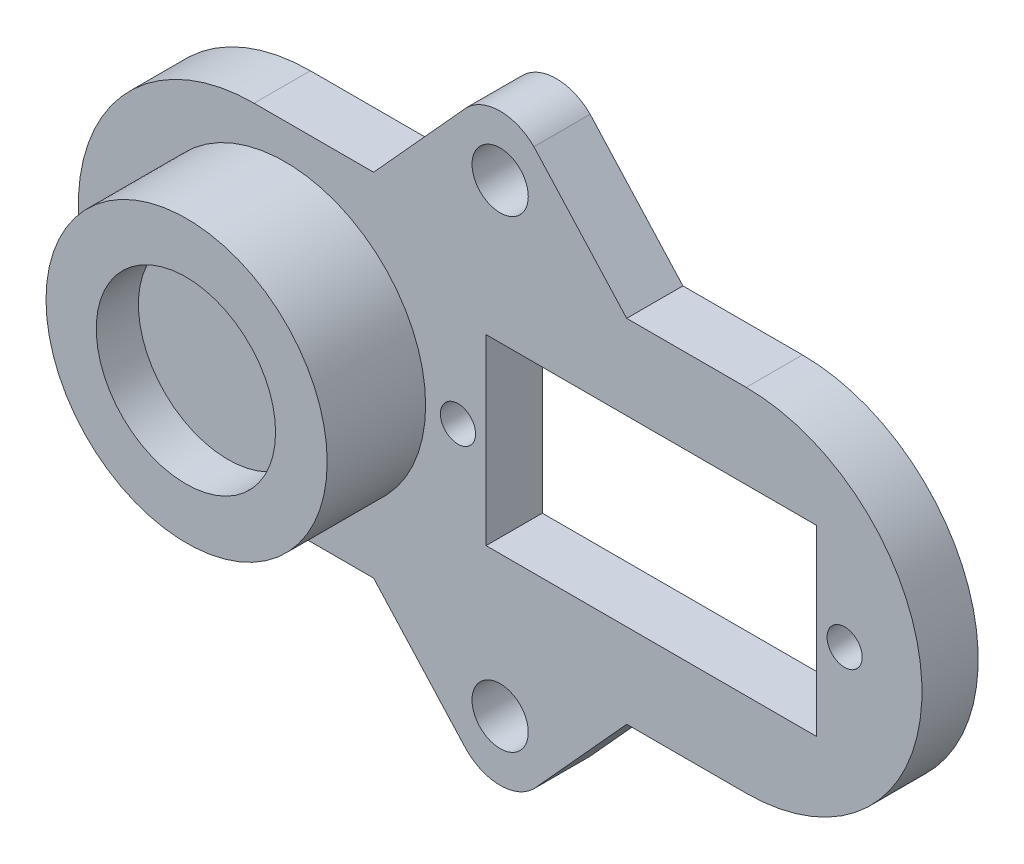
SolidWorks part; units mm, degrees
ref_plane "Front" through (0, 0, 0) normal (0, 0, 1) x (1, 0, 0)
ref_plane "Top" through (0, 0, 0) normal (0, 1, 0) x (1, 0, 0)
ref_plane "Right" through (0, 0, 0) normal (1, 0, 0) x (0, 0, -1)
sketch "Sketch1" plane through (0, 0, 0) normal (0, 0, 1) x (1, 0, 0)
  line L0 (-9, 12.5) -> (-2.401, 19.7724)
  line L1 (-17.5, 12.5) -> (-9, 12.5)
  line L5 (2.401, 19.7724) -> (9, 12.5)
  line L6 (9, 12.5) -> (17.5, 12.5)
  line L7 (-52.4135, 0) -> (76.2531, 0) construction
  line L12 (9, -12.5) -> (17.5, -12.5)
  line L13 (2.401, -19.7724) -> (9, -12.5)
  line L14 (-17.5, -12.5) -> (-9, -12.5)
  line L15 (-9, -12.5) -> (-2.401, -19.7724)
  line L19 (0, 44.7347) -> (0, -34.4115) construction
  line L24 (-1, 6.5) -> (22.5, 6.5)
  line L25 (-1, 6.5) -> (-1, -6.5)
  line L26 (-1, -6.5) -> (22.5, -6.5)
  line L27 (22.5, 6.5) -> (22.5, -6.5)
  circle A2 centre (0, 16.5) radius 2
  arc A4 (-2.401, 19.7724) -> (2.401, 19.7724) centre (0, 17.3714) cw
  arc A5 (-2.401, -19.7724) -> (2.401, -19.7724) centre (0, -17.3714) ccw
  circle A6 centre (0, -16.5) radius 2
  arc A11 (17.5, -12.5) -> (17.5, 12.5) centre (17.5, 0) ccw
  arc A12 (-17.5, 12.5) -> (-17.5, -12.5) centre (-17.5, 0) ccw
  circle A13 centre (-3, 0) radius 1.25
  circle A14 centre (24.5, 0) radius 1.25
  point P32 (-1, 0)
  dimension "D3" = 17.5
  dimension "D4" = 17.5
  dimension "D9" = 4
  dimension "D10" = 13
  dimension "D5" = 2.5
  dimension "D6" = 27.5
  dimension "D2" = 12.5
  dimension "D1" = 2.5
  dimension "D7" = 3
  dimension "D8" = 23.5
  dimension "D11" = 2
extrude "Boss-Extrude1" add sketch "Sketch1" along normal blind 4
sketch "Sketch3" plane through (0, 0, 4) normal (0, 0, 1) x (1, 0, 0)
  circle A0 centre (-15.3, 0) radius 10
  dimension "D1" = 20
  dimension "D2" = 15.3
extrude "Boss-Extrude2" add sketch "Sketch3" along normal blind 7
sketch "Sketch4" plane through (0, 0, 11) normal (0, 0, 1) x (1, 0, 0)
  circle A0 centre (-15.35, 0) radius 6.3775
  point P2 (0, 0)
extrude "Cut-Extrude1" cut sketch "Sketch4" against normal blind 3
